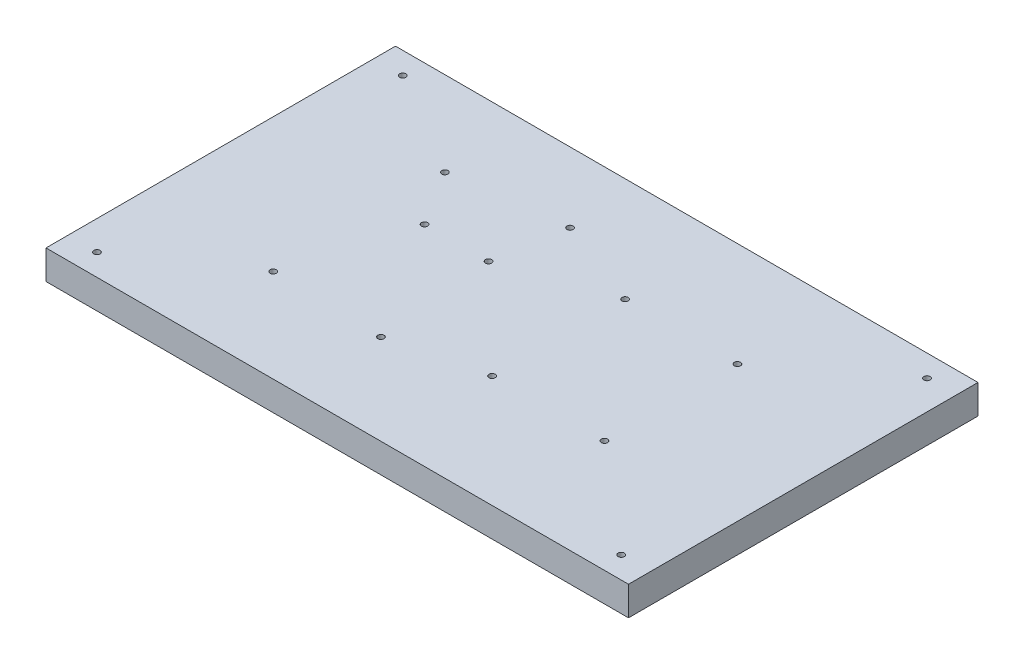
SolidWorks part; units mm, degrees
material "ABS"
ref_plane "Plan de face" through (0, 0, 0) normal (0, 0, 1) x (1, 0, 0)
ref_plane "Plan de dessus" through (0, 0, 0) normal (0, 1, 0) x (1, 0, 0)
ref_plane "Plan de droite" through (0, 0, 0) normal (1, 0, 0) x (0, 0, -1)
sketch "Esquisse1" plane through (0, 0, 0) normal (0, 1, 0) x (1, 0, 0)
  line L0 (0, 0) -> (0, 152.4)
  line L1 (0, 152.4) -> (254, 152.4)
  line L2 (254, 152.4) -> (254, 0)
  line L3 (0, 0) -> (254, 0)
  dimension "D1" = 254
  dimension "D2" = 152.4
extrude "Boss.-Extru.1" add sketch "Esquisse1" along normal blind 12.7
hole_wizard "Dégagement M2.51" positions "Esquisse3" profile "Esquisse4" hole size "M2.5" standard "Ansi Metric"
sketch "Esquisse3" plane through (0, 12.7, 0) normal (0, 1, 0) x (1, 0, 0)
  line L0 (254, 0) -> (254, 152.4) construction
  line L3 (0, 0) -> (254, 0) construction
  point P0 (194.62, 48.9)
  point P2 (194.62, 106.9)
  point P4 (145.62, 106.9)
  point P6 (145.62, 48.9)
  point P25 (106.64, 121.87)
  point P28 (58.42, 115.51)
  point P31 (101.56, 91.42)
  point P34 (73.65, 91.42)
  point P37 (58.42, 40.63)
  point P40 (106.64, 39.4)
  dimension "D1" = 59.38
  dimension "D2" = 58
  dimension "D3" = 49
  dimension "D4" = 48.9
sketch "Esquisse4" plane through (194.62, 12.7, -48.9) normal (1, 0, 0) x (0, 0, 1)
  line L0 (0, 0) -> (0, 8.89)
  line L1 (0, 8.89) -> (1.35, 8.89)
  line L2 (1.35, 8.89) -> (1.35, 0)
  line L5 (1.35, 0) -> (0, 0)
  line L10 (0, 8.89) -> (-1.35, 8.89) construction
  line L11 (0, -6.35) -> (0, 107.95) construction
  dimension "Diamètre du perçage" = 2.7
  dimension "Profondeur du perçage" = 8.89
  dimension "Angle de pointe" = 180
hole_wizard "Dégagement M2.52" positions "Esquisse5" profile "Esquisse6" hole size "M2.5" standard "Ansi Metric"
sketch "Esquisse5" plane through (0, 12.7, 0) normal (0, 1, 0) x (1, 0, 0)
  point P0 (12.7, 9.525)
  point P3 (241.3, 9.525)
  point P6 (241.3, 142.875)
  point P9 (12.7, 142.875)
sketch "Esquisse6" plane through (12.7, 12.7, -9.525) normal (1, 0, 0) x (0, 0, 1)
  line L0 (0, 0) -> (0, 95.25)
  line L1 (0, 95.25) -> (1.35, 95.25)
  line L2 (1.35, 95.25) -> (1.35, 0)
  line L5 (1.35, 0) -> (0, 0)
  line L10 (0, 95.25) -> (-1.35, 95.25) construction
  line L11 (0, -6.35) -> (0, 107.95) construction
  dimension "Diamètre du perçage" = 2.7
  dimension "Profondeur du perçage" = 95.25
  dimension "Angle de pointe" = 180
